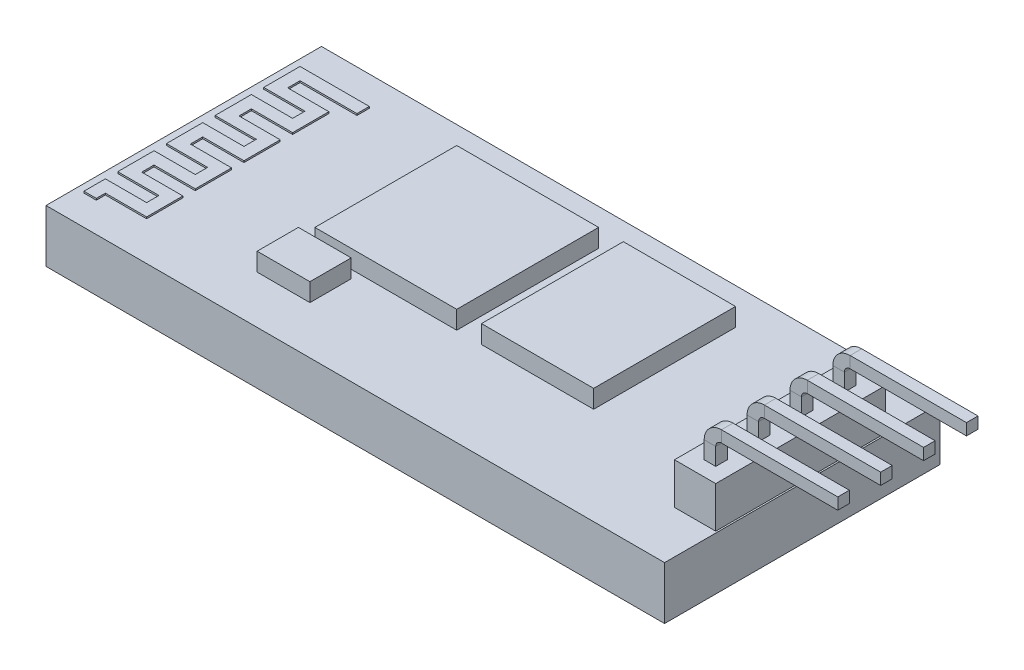
SolidWorks part; units mm, degrees
ref_plane "Front Plane" through (0, 0, 0) normal (0, 0, 1) x (1, 0, 0)
ref_plane "Top Plane" through (0, 0, 0) normal (0, 1, 0) x (1, 0, 0)
ref_plane "Right Plane" through (0, 0, 0) normal (1, 0, 0) x (0, 0, -1)
sketch "Sketch1" plane through (0, 0, 0) normal (0, 1, 0) x (1, 0, 0)
  line L1 (-18.75, -8.35) -> (18.75, -8.35)
  line L2 (-18.75, -8.35) -> (-18.75, 8.35)
  line L3 (-18.75, 8.35) -> (18.75, 8.35)
  line L4 (18.75, -8.35) -> (18.75, 8.35)
  line L5 (-18.75, -8.35) -> (18.75, 8.35) construction
  line L6 (-18.75, 8.35) -> (18.75, -8.35) construction
  point P0 (0, 0)
  dimension "D1" = 16.7
  dimension "D2" = 37.5
extrude "Boss-Extrude1" add sketch "Sketch1" along normal blind 3.2
sketch "Sketch2" plane through (0, 3.2, 0) normal (0, 1, 0) x (1, 0, 0)
  line L0 (18.75, -8.35) -> (18.75, 8.35) construction
  line L1 (-8.35, -2.45) -> (0.25, -2.45)
  line L2 (-8.35, -2.45) -> (-8.35, 6.15)
  line L3 (-8.35, 6.15) -> (0.25, 6.15)
  line L4 (0.25, -2.45) -> (0.25, 6.15)
  line L5 (-8.35, -2.45) -> (0.25, 6.15) construction
  line L6 (-8.35, 6.15) -> (0.25, -2.45) construction
  line L7 (8.55, 6.15) -> (1.75, 6.15)
  line L8 (8.55, 6.15) -> (8.55, -2.45)
  line L9 (8.55, -2.45) -> (1.75, -2.45)
  line L10 (1.75, 6.15) -> (1.75, -2.45)
  line L11 (8.55, 6.15) -> (1.75, -2.45) construction
  line L12 (8.55, -2.45) -> (1.75, 6.15) construction
  line L13 (-8.85, -5.45) -> (-5.65, -5.45)
  line L14 (-8.85, -5.45) -> (-8.85, -2.95)
  line L15 (-8.85, -2.95) -> (-5.65, -2.95)
  line L16 (-5.65, -5.45) -> (-5.65, -2.95)
  line L17 (-8.85, -5.45) -> (-5.65, -2.95) construction
  line L18 (-8.85, -2.95) -> (-5.65, -5.45) construction
  line L20 (18.75, 8.35) -> (-18.75, 8.35) construction
  point P0 (-4.05, 1.85)
  point P5 (5.15, 1.85)
  point P10 (-7.25, -4.2)
  dimension "D1" = 6.8
  dimension "D2" = 8.6
  dimension "D3" = 8.6
  dimension "D4" = 8.6
  dimension "D5" = 2.5
  dimension "D6" = 3.2
  dimension "D7" = 10.2
  dimension "D8" = 2.2
  dimension "D9" = 2.2
  dimension "D10" = 1.5
  dimension "D11" = 0.5
  dimension "D12" = 0.5
extrude "Boss-Extrude2" add sketch "Sketch2" along normal blind 1.1
sketch "Sketch3" plane through (0, 3.2, 0) normal (0, 1, 0) x (1, 0, 0)
  line L0 (-14.05, 6.55) -> (-18.25, 6.55)
  line L1 (-18.25, 6.55) -> (-18.25, 4.35)
  line L2 (-18.25, 4.35) -> (-15.75, 4.35)
  line L3 (-15.75, 4.35) -> (-15.75, 3.6)
  line L4 (-15.75, 3.6) -> (-18.25, 3.6)
  line L5 (-18.25, 3.6) -> (-18.25, 1.4)
  line L6 (-18.25, 1.4) -> (-15.75, 1.4)
  line L7 (-15.75, 1.4) -> (-15.75, 0.65)
  line L8 (-15.75, 0.65) -> (-18.25, 0.65)
  line L9 (-18.25, 0.65) -> (-18.25, -1.55)
  line L10 (-18.25, -1.55) -> (-15.75, -1.55)
  line L11 (-15.75, -1.55) -> (-15.75, -2.3)
  line L12 (-15.75, -2.3) -> (-18.25, -2.3)
  line L13 (-18.25, -2.3) -> (-18.25, -4.5)
  line L14 (-18.25, -4.5) -> (-15.75, -4.5)
  line L15 (-15.75, -4.5) -> (-15.75, -5.25)
  line L16 (-15.75, -5.25) -> (-18.25, -5.25)
  line L17 (-18.25, -5.25) -> (-18.25, -6.55)
  line L18 (-18.25, -6.55) -> (-17.5, -6.55)
  line L19 (-15, -6) -> (-15, -3.8)
  line L20 (-15, -3.8) -> (-17.5, -3.8)
  line L21 (-17.5, -3.8) -> (-17.5, -3.05)
  line L22 (-17.5, -3.05) -> (-15, -3.05)
  line L23 (-15, -3.05) -> (-15, -0.85)
  line L24 (-17.5, -6.55) -> (-17.5, -6)
  line L25 (-15, -0.1) -> (-17.5, -0.1)
  line L26 (-17.5, -0.1) -> (-17.5, -0.85)
  line L27 (-17.5, -6) -> (-15, -6)
  line L28 (-17.5, -0.85) -> (-15, -0.85)
  line L29 (-18.75, -8.35) -> (18.75, -8.35) construction
  line L30 (-15, 2.85) -> (-17.5, 2.85)
  line L31 (-15, 2.85) -> (-15, 5.05)
  line L32 (-15, 5.05) -> (-17.5, 5.05)
  line L33 (-17.5, 5.05) -> (-17.5, 5.8)
  line L34 (-17.5, 5.8) -> (-14.05, 5.8)
  line L35 (-14.05, 5.8) -> (-14.05, 6.55)
  line L36 (18.75, 8.35) -> (-18.75, 8.35) construction
  line L37 (-18.75, 8.35) -> (-18.75, -8.35) construction
  line L38 (-17.5, 2.85) -> (-17.5, 2.1)
  line L39 (-17.5, 2.1) -> (-15, 2.1)
  line L40 (-15, 2.1) -> (-15, -0.1)
  dimension "D1" = 1.8
  dimension "D2" = 2.2
  dimension "D3" = 0.75
  dimension "D4" = 0.75
  dimension "D5" = 0.5
  dimension "D6" = 4.2
  dimension "D7" = 2.5
  dimension "D8" = 0.75
  dimension "D9" = 1.8
extrude "Boss-Extrude3" add sketch "Sketch3" along normal blind 0.1
sketch "Sketch4" plane through (0, 3.2, 0) normal (0, 1, 0) x (1, 0, 0)
  line L1 (16.15, -5.15) -> (18.65, -5.15)
  line L2 (16.15, -5.15) -> (16.15, 5.15)
  line L3 (16.15, 5.15) -> (18.65, 5.15)
  line L4 (18.65, -5.15) -> (18.65, 5.15)
  line L5 (16.15, -5.15) -> (18.65, 5.15) construction
  line L6 (16.15, 5.15) -> (18.65, -5.15) construction
  line L7 (16.15, 0) -> (0, 0) construction
  line L8 (18.75, -8.35) -> (18.75, 8.35) construction
  point P0 (17.4, 0)
  dimension "D1" = 2.5
  dimension "D2" = 10.3
  dimension "D3" = 0.1
extrude "Boss-Extrude4" add sketch "Sketch4" along normal blind 2.5
sketch "Sketch5" plane through (0, 5.7, 0) normal (0, 1, 0) x (1, 0, 0)
  line L0 (16.15, 5.15) -> (16.15, -5.15) construction
  line L1 (16.15, 2.55) -> (18.65, 2.55)
  line L2 (16.15, 2.55) -> (16.15, 2.65)
  line L3 (16.15, 2.65) -> (18.65, 2.65)
  line L4 (18.65, 2.55) -> (18.65, 2.65)
  line L5 (16.15, 2.55) -> (18.65, 2.65) construction
  line L6 (16.15, 2.65) -> (18.65, 2.55) construction
  line L7 (16.15, -2.65) -> (18.65, -2.65)
  line L8 (16.15, -2.65) -> (16.15, -2.55)
  line L9 (16.15, -2.55) -> (18.65, -2.55)
  line L10 (18.65, -2.65) -> (18.65, -2.55)
  line L11 (16.15, -2.65) -> (18.65, -2.55) construction
  line L12 (16.15, -2.55) -> (18.65, -2.65) construction
  line L13 (16.15, -0.05) -> (18.65, -0.05)
  line L14 (16.15, -0.05) -> (16.15, 0.05)
  line L15 (16.15, 0.05) -> (18.65, 0.05)
  line L16 (18.65, -0.05) -> (18.65, 0.05)
  line L17 (16.15, -0.05) -> (18.65, 0.05) construction
  line L18 (16.15, 0.05) -> (18.65, -0.05) construction
  line L19 (18.65, -5.15) -> (18.65, 5.15) construction
  line L20 (18.65, 5.15) -> (16.15, 5.15) construction
  line L21 (16.15, -5.15) -> (18.65, -5.15) construction
  point P0 (17.4, 2.6)
  point P5 (17.4, -2.6)
  point P10 (17.4, 0)
  dimension "D1" = 0.1
  dimension "D2" = 2.5
  dimension "D3" = 2.5
  dimension "D4" = 2.5
extrude "Cut-Extrude1" cut sketch "Sketch5" against normal blind 0.2
sketch "Sketch6" plane through (0, 5.7, 0) normal (0, 1, 0) x (1, 0, 0)
  line L0 (16.15, 5.15) -> (18.65, 2.65) construction
  line L1 (16.15, 2.55) -> (18.65, 0.05) construction
  line L2 (18.65, 0.05) -> (16.15, 0.05) construction
  line L3 (18.65, 0.05) -> (16.15, 0.05) construction
  line L4 (16.15, -0.05) -> (18.65, -2.55) construction
  line L5 (18.65, -5.15) -> (18.65, 5.15) construction
  line L6 (18.65, -2.55) -> (16.15, -2.55) construction
  line L7 (16.15, -2.65) -> (18.65, -5.15) construction
  line L9 (17.05, 3.55) -> (17.75, 3.55)
  line L10 (17.05, 3.55) -> (17.05, 4.25)
  line L11 (17.05, 4.25) -> (17.75, 4.25)
  line L12 (17.75, 3.55) -> (17.75, 4.25)
  line L13 (17.05, 3.55) -> (17.75, 4.25) construction
  line L14 (17.05, 4.25) -> (17.75, 3.55) construction
  line L15 (17.05, 0.95) -> (17.75, 0.95)
  line L16 (17.05, 0.95) -> (17.05, 1.65)
  line L17 (17.05, 1.65) -> (17.75, 1.65)
  line L18 (17.75, 0.95) -> (17.75, 1.65)
  line L19 (17.05, 0.95) -> (17.75, 1.65) construction
  line L20 (17.05, 1.65) -> (17.75, 0.95) construction
  line L21 (17.05, -1.65) -> (17.75, -1.65)
  line L22 (17.05, -1.65) -> (17.05, -0.95)
  line L23 (17.05, -0.95) -> (17.75, -0.95)
  line L24 (17.75, -1.65) -> (17.75, -0.95)
  line L25 (17.05, -1.65) -> (17.75, -0.95) construction
  line L26 (17.05, -0.95) -> (17.75, -1.65) construction
  line L27 (17.05, -4.25) -> (17.75, -4.25)
  line L28 (17.05, -4.25) -> (17.05, -3.55)
  line L29 (17.05, -3.55) -> (17.75, -3.55)
  line L30 (17.75, -4.25) -> (17.75, -3.55)
  line L31 (17.05, -4.25) -> (17.75, -3.55) construction
  line L32 (17.05, -3.55) -> (17.75, -4.25) construction
  point P22 (17.4, 3.9)
  point P28 (17.4, 1.3)
  point P33 (17.4, -1.3)
  point P38 (17.4, -3.9)
  dimension "D1" = 0.7
sketch "Sketch7" plane through (0, 0, 0) normal (0, 0, 1) x (1, 0, 0)
  line L0 (17.4, 5.7) -> (17.4, 6.75)
  line L1 (18.1, 7.45) -> (25.15, 7.45)
  line L2 (16.15, 5.7) -> (18.65, 5.7) construction
  line L3 (18.65, 5.7) -> (18.65, 3.2) construction
  arc A0 (17.4, 6.75) -> (18.1, 7.45) centre (18.1, 6.75) cw
  dimension "D1" = 1.75
  dimension "D3" = 0.7
  dimension "D2" = 6.5
sweep "Sweep1" add profiles "Sketch6" path "Sketch7"
